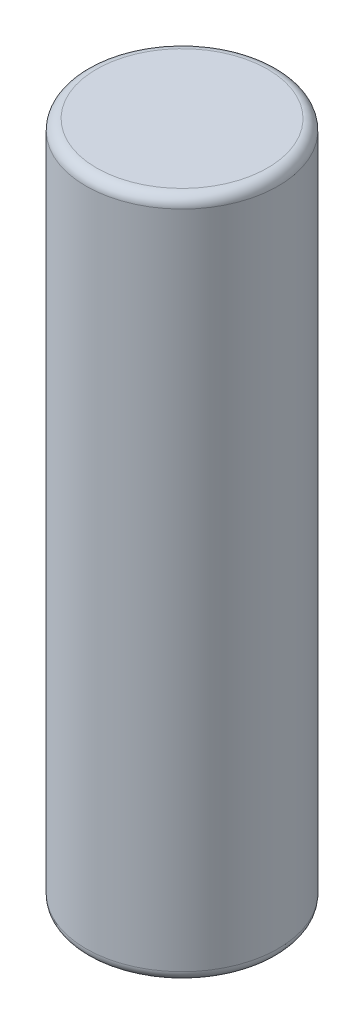
SolidWorks part; units mm, degrees
ref_plane "Front Plane" through (0, 0, 0) normal (0, 0, 1) x (1, 0, 0)
ref_plane "Top Plane" through (0, 0, 0) normal (0, 1, 0) x (1, 0, 0)
ref_plane "Right Plane" through (0, 0, 0) normal (1, 0, 0) x (0, 0, -1)
sketch "Sketch1" plane through (0, 0, 0) normal (0, 1, 0) x (1, 0, 0)
  circle A0 centre (0, 0) radius 9.15
  dimension "D1" = 18.3
extrude "Boss-Extrude1" add sketch "Sketch1" along normal blind 64.9
fillet "Fillet1" radius 1 2 edges at (0, 64.9, 9.15) (0, 0, 9.15)
